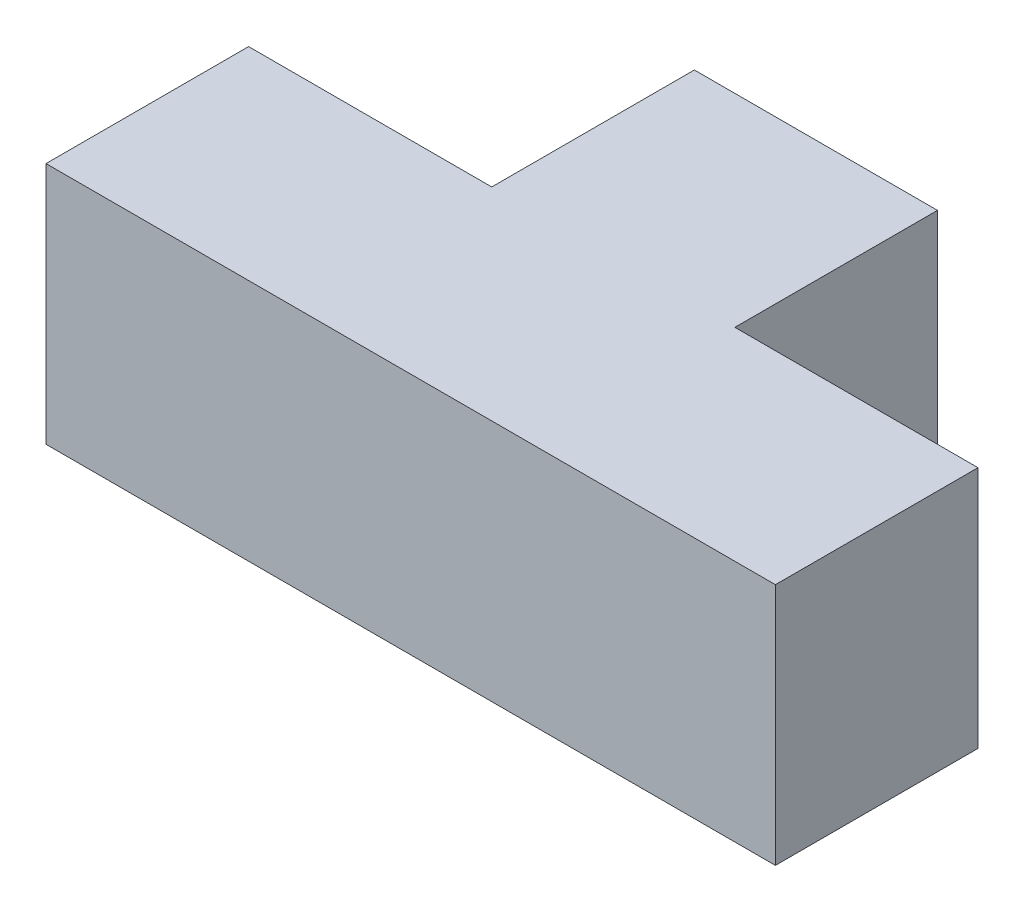
SolidWorks part; units mm, degrees
ref_plane "Front Plane" through (0, 0, 0) normal (0, 0, 1) x (1, 0, 0)
ref_plane "Top Plane" through (0, 0, 0) normal (0, 1, 0) x (1, 0, 0)
ref_plane "Right Plane" through (0, 0, 0) normal (1, 0, 0) x (0, 0, -1)
sketch "Sketch2" plane through (0, 0, 0) normal (0, 1, 0) x (1, 0, 0)
  line L0 (-45, 0) -> (45, 0)
  line L1 (45, 0) -> (45, 25)
  line L2 (45, 25) -> (15, 25)
  line L3 (15, 25) -> (15, 50)
  line L4 (15, 50) -> (-15, 50)
  line L5 (0, 0) -> (0, 65.5367) construction
  line L6 (-15, 25) -> (-15, 50)
  line L7 (-45, 25) -> (-15, 25)
  line L8 (-45, 0) -> (-45, 25)
  point P9 (0, 50)
  dimension "D1" = 45
  dimension "D3" = 15
  dimension "D4" = 50
  dimension "D5" = 25
extrude "Boss-Extrude1" add sketch "Sketch2" along normal blind 30
